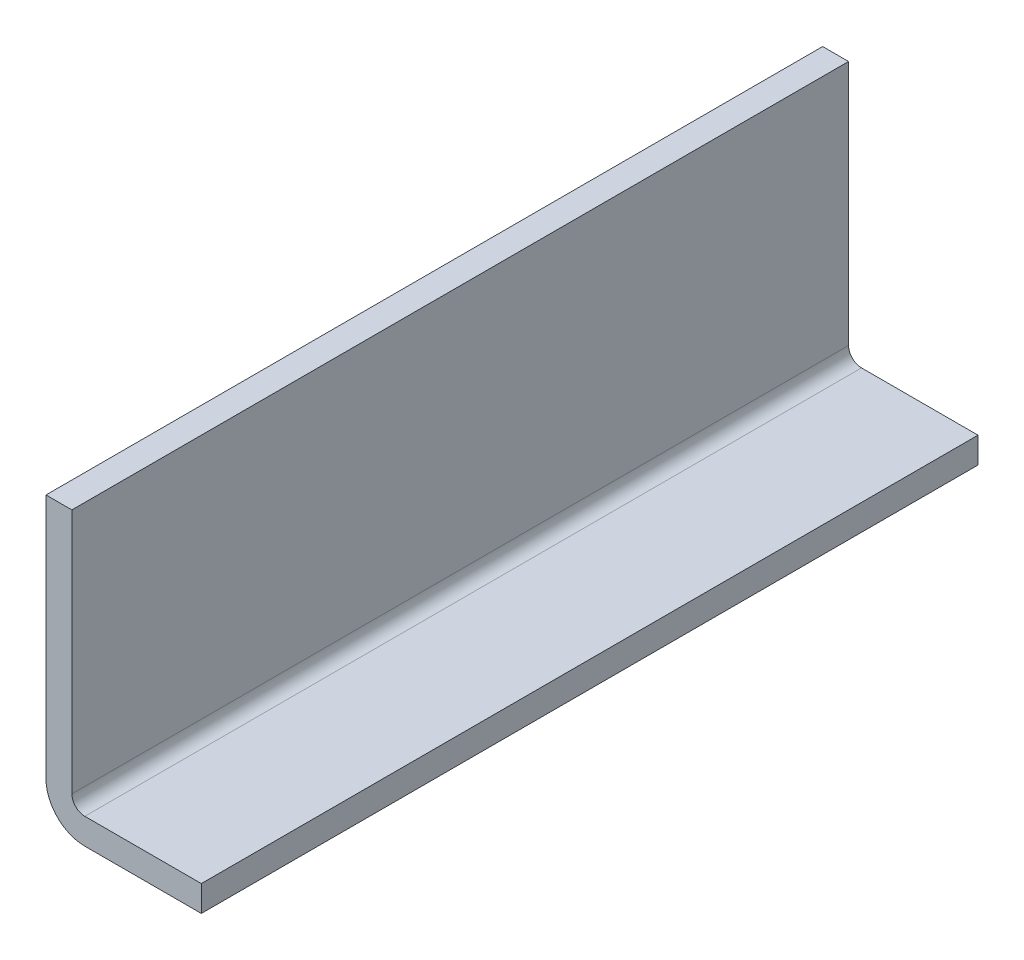
SolidWorks part; units mm, degrees
ref_plane "Plan de face" through (0, 0, 0) normal (0, 0, 1) x (1, 0, 0)
ref_plane "Plan de dessus" through (0, 0, 0) normal (0, 1, 0) x (1, 0, 0)
ref_plane "Plan de droite" through (0, 0, 0) normal (1, 0, 0) x (0, 0, -1)
sketch "Esquisse1" plane through (0, 0, 0) normal (0, 0, 1) x (1, 0, 0)
  line L0 (0, 20) -> (0, 1)
  line L1 (1, 0) -> (10, 0)
  line L2 (-2, 20) -> (-2, 1)
  line L3 (1, -2) -> (10, -2)
  line L4 (-2, 20) -> (0, 20)
  line L5 (10, 0) -> (10, -2)
  line L6 (0, 20) -> (0, 0) construction
  line L7 (0, 0) -> (10, 0) construction
  line L8 (-2, -2) -> (10, -2) construction
  line L9 (-2, 20) -> (-2, -2) construction
  arc A0 (0, 1) -> (1, 0) centre (1, 1) ccw
  arc A1 (1, -2) -> (-2, 1) centre (1, 1) cw
  point P11 (0, 0)
  dimension "D2" = 1
  dimension "D1" = 2
extrude "Extrusion1" add sketch "Esquisse1" along normal blind 60
